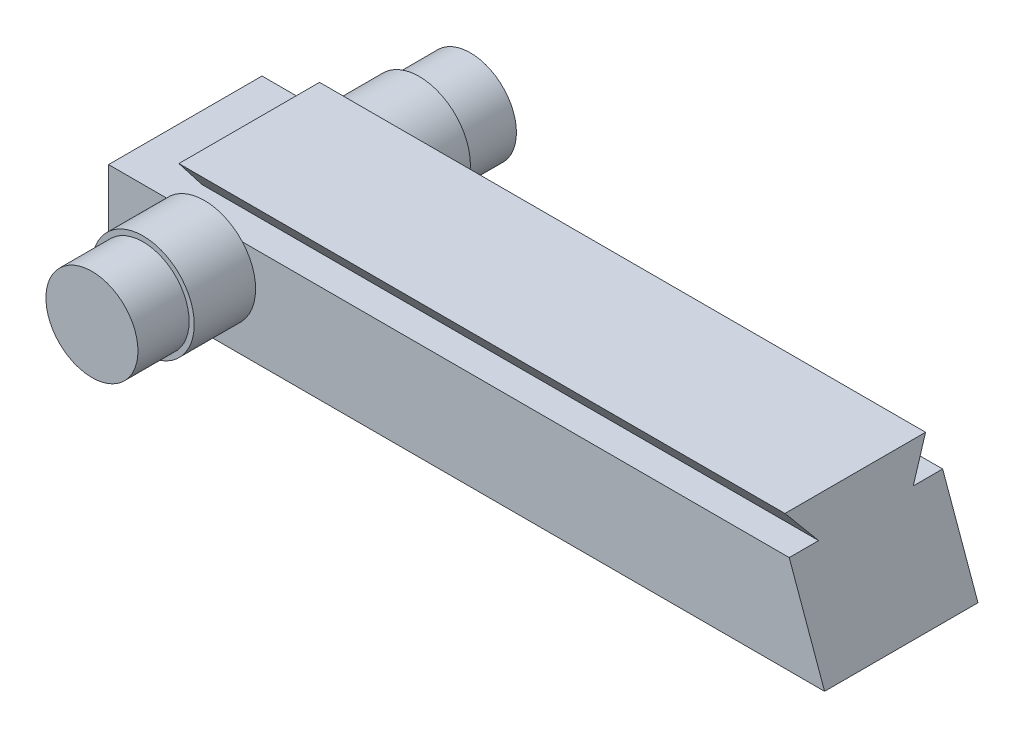
SolidWorks part; units mm, degrees
ref_plane "Front Plane" through (0, 0, 0) normal (0, 0, 1) x (1, 0, 0)
ref_plane "Top Plane" through (0, 0, 0) normal (0, 1, 0) x (1, 0, 0)
ref_plane "Right Plane" through (0, 0, 0) normal (1, 0, 0) x (0, 0, -1)
sketch "Sketch1" plane through (0, 0, 0) normal (1, 0, 0) x (0, 0, -1)
  line L1 (-3.81, -2.4384) -> (3.81, -2.4384)
  line L2 (-3.81, -2.4384) -> (-3.81, 2.4384)
  line L3 (-3.81, 2.4384) -> (3.81, 2.4384)
  line L4 (3.81, -2.4384) -> (3.81, 2.4384)
  line L5 (-3.81, -2.4384) -> (3.81, 2.4384) construction
  line L6 (-3.81, 2.4384) -> (3.81, -2.4384) construction
  point P0 (0, 0)
  dimension "D1" = 4.8768
  dimension "D2" = 7.62
extrude "Boss-Extrude1" add sketch "Sketch1" along normal mid plane 35.56
sketch "Sketch2" plane through (17.78, 0, 0) normal (1, 0, 0) x (0, 0, -1)
  line L0 (-3.4925, 3.9116) -> (3.4925, 3.9116)
  line L1 (3.4925, 3.9116) -> (2.3495, 2.4384)
  line L2 (3.81, 2.4384) -> (-3.81, 2.4384) construction
  line L3 (-3.4925, 3.9116) -> (-2.3495, 2.4384)
  line L4 (0, 0) -> (0, -50000) construction
  line L7 (-2.3495, 2.4384) -> (2.3495, 2.4384)
  dimension "D1" = 6.985
  dimension "D2" = 4.699
  dimension "D3" = 1.4732
extrude "Boss-Extrude2" add sketch "Sketch2" against normal blind 32.385
sketch "Sketch3" plane through (0, 0, 3.81) normal (0, 0, 1) x (1, 0, 0)
  line L0 (17.78, -2.4384) -> (15.494, 3.9116)
  line L1 (-14.605, 3.9116) -> (17.78, 3.9116) construction
  line L2 (15.494, 3.9116) -> (17.78, 3.9116)
  line L3 (17.78, 3.9116) -> (17.78, -2.4384)
  dimension "D1" = 2.286
extrude "Cut-Extrude1" cut sketch "Sketch3" against normal through all
sketch "Sketch5" plane through (0, 0, 3.81) normal (0, 0, 1) x (1, 0, 0)
  circle A0 centre (-13.0175, 0.7366) radius 2.54
  dimension "D1" = 5.08
extrude "Boss-Extrude3" add sketch "Sketch5" along normal blind 3.048
sketch "Sketch7" plane through (0, 0, 6.858) normal (0, 0, 1) x (1, 0, 0)
  circle A0 centre (-13.0175, 0.7366) radius 2.286
  dimension "D1" = 4.572
extrude "Boss-Extrude4" add sketch "Sketch7" along normal blind 2.54
mirror "Mirror1" about plane through (0, 0, 0) normal (0, 0, 1) of "Boss-Extrude3", "Boss-Extrude4"
